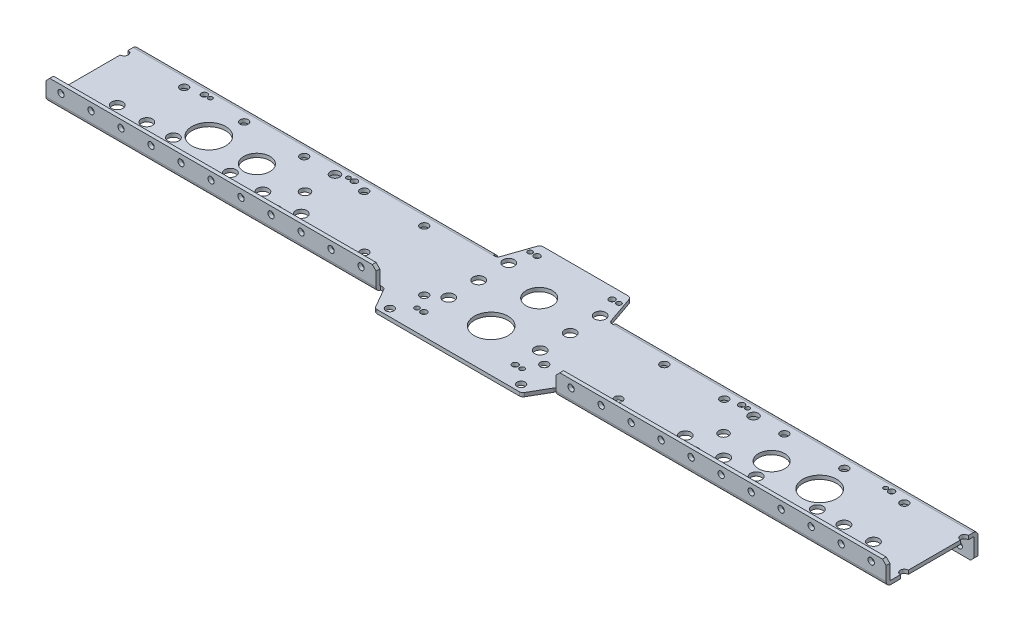
SolidWorks part; units mm, degrees
ref_plane "Front Plane" through (0, 0, 0) normal (0, 0, 1) x (1, 0, 0)
ref_plane "Top Plane" through (0, 0, 0) normal (0, 1, 0) x (1, 0, 0)
ref_plane "Right Plane" through (0, 0, 0) normal (1, 0, 0) x (0, 0, -1)
ref_plane "Plane1" through (0, 3.175, 0) normal (0, 1, 0) x (1, 0, 0)
sketch "Sketch1" plane through (0, 3.175, 0) normal (0, 1, 0) x (1, 0, 0)
  line L0 (50.8, -3.937) -> (355.6, -3.937)
  line L1 (355.6, -3.937) -> (355.6, 73.787)
  line L2 (355.6, 73.787) -> (50.8, 73.787)
  line L3 (50.8, 73.787) -> (50.8, -3.937)
extrude "Boss-Extrude1" add sketch "Sketch1" against normal blind 22.225
sketch "Sketch2" plane through (50.8, 0, 0) normal (-1, 0, 0) x (0, 0, 1)
  line L0 (3.937, -19.05) -> (3.937, 0)
  line L1 (3.937, 0) -> (-70.612, 0)
  line L2 (-70.612, 0) -> (-70.612, -19.05)
  line L3 (-70.612, -19.05) -> (3.937, -19.05)
extrude "Cut-Extrude1" cut sketch "Sketch2" against normal through all
sketch "Sketch3" plane through (355.6, 0, 0) normal (1, 0, 0) x (0, 0, -1)
  line L0 (69.85, 0) -> (-3.937, 0)
  line L1 (-3.937, 0) -> (-3.937, 3.175)
  line L2 (-3.937, 3.175) -> (69.85, 3.175)
  line L3 (69.85, 3.175) -> (69.85, 0)
extrude "Boss-Extrude2" add sketch "Sketch3" along normal blind 406.4
sketch "Sketch4" plane through (0, 0, -69.85) normal (0, 0, -1) x (-1, 0, 0)
  line L0 (-762, 0) -> (-762, 3.175)
  line L1 (-762, 3.175) -> (-457.2, 3.175)
  line L2 (-457.2, 3.175) -> (-457.2, 0)
  line L3 (-457.2, 0) -> (-762, 0)
extrude "Boss-Extrude3" add sketch "Sketch4" along normal blind 3.937
sketch "Sketch5" plane through (0, 0, 0) normal (0, -1, 0) x (1, 0, 0)
  line L0 (457.2, -70.612) -> (762, -70.612)
  line L1 (762, -70.612) -> (762, -73.787)
  line L2 (762, -73.787) -> (457.2, -73.787)
  line L3 (457.2, -73.787) -> (457.2, -70.612)
extrude "Boss-Extrude4" add sketch "Sketch5" along normal blind 19.05
sketch "Sketch6" plane through (0, 3.175, 0) normal (0, 1, 0) x (-1, 0, 0)
  line L0 (-482.6, 3.937) -> (-482.6, 0)
  line L1 (-482.6, 0) -> (-50.8, 0)
  line L2 (-50.8, 0) -> (-50.8, 3.937)
  line L3 (-50.8, 3.937) -> (-482.6, 3.937)
extrude "Cut-Extrude2" cut sketch "Sketch6" against normal through all
sketch "Sketch7" plane through (0, 3.175, 0) normal (0, 1, 0) x (-1, 0, 0)
  line L0 (-762, 3.937) -> (-482.6, 3.937)
  line L1 (-482.6, 3.937) -> (-482.6, 0.762)
  line L2 (-482.6, 0.762) -> (-762, 0.762)
  line L3 (-762, 0.762) -> (-762, 3.937)
extrude "Boss-Extrude5" add sketch "Sketch7" along normal blind 15.875
sketch "Sketch8" plane through (0, 0, 0) normal (0, 0, 1) x (1, 0, 0)
  line L0 (330.2, 3.175) -> (330.2, 0)
  line L1 (330.2, 0) -> (50.8, 0)
  line L2 (50.8, 0) -> (50.8, 3.175)
  line L3 (50.8, 3.175) -> (330.2, 3.175)
extrude "Boss-Extrude6" add sketch "Sketch8" along normal blind 3.937
sketch "Sketch9" plane through (0, 3.175, 0) normal (0, 1, 0) x (-1, 0, 0)
  line L0 (-50.8, 0.762) -> (-330.2, 0.762)
  line L1 (-330.2, 0.762) -> (-330.2, 3.937)
  line L2 (-330.2, 3.937) -> (-50.8, 3.937)
  line L3 (-50.8, 3.937) -> (-50.8, 0.762)
extrude "Boss-Extrude7" add sketch "Sketch9" along normal blind 15.875
sketch "Sketch10" plane through (0, 0, -69.85) normal (0, 0, -1) x (-1, 0, 0)
  line L0 (-368.2206, 0) -> (-444.5794, 0)
  line L1 (-444.5794, 0) -> (-444.5794, 3.175)
  line L2 (-444.5794, 3.175) -> (-368.2206, 3.175)
  line L3 (-368.2206, 3.175) -> (-368.2206, 0)
extrude "Boss-Extrude8" add sketch "Sketch10" along normal blind 27.432
sketch "Sketch11" plane through (0, 0, 0) normal (0, 0, 1) x (1, 0, 0)
  line L0 (468.4265, 0) -> (344.3735, 0)
  line L1 (344.3735, 0) -> (344.3735, 3.175)
  line L2 (344.3735, 3.175) -> (468.4265, 3.175)
  line L3 (468.4265, 3.175) -> (468.4265, 0)
extrude "Boss-Extrude9" add sketch "Sketch11" along normal blind 19.05
draft "Draft1" type of draft neutral plane draft angle 30 faces to draft 2 face at (344.3735, 1.5875, 9.525) face at (468.4265, 1.5875, 9.525) neutral plane through (0, 0, 19.05) neutral plane normal (0, 0, 1) parameters "D1"=30
draft "Draft2" type of draft neutral plane draft angle 19 faces to draft 2 face at (444.5794, 1.5875, -83.566) face at (368.2206, 1.5875, -83.566) neutral plane through (0, 0, -97.282) neutral plane normal (0, 0, -1) parameters "D1"=19
hole_wizard "M8 Clearance Hole1" positions "Sketch13" profile "Sketch12" hole size "M8" standard "ANSI Metric"
sketch "Sketch13" plane through (0, 0, 0) normal (0, -1, 0) x (-1, 0, 0)
  point P0 (-367.6757, 70.866)
  point P1 (-367.6757, 20.066)
  point P2 (-445.1243, 20.066)
  point P3 (-445.1243, 70.866)
  point P4 (-367.6757, 45.466)
  point P5 (-445.1243, 45.466)
  point P6 (-628.9477, 19.05)
  point P7 (-601.4385, 19.05)
  point P8 (-568.9249, 19.05)
  point P9 (-243.8751, 19.05)
  point P10 (-211.3615, 19.05)
  point P11 (-183.8523, 19.05)
  point P12 (-678.9442, 20.828)
  point P13 (-701.4504, 20.828)
  point P14 (-726.4609, 20.828)
  point P15 (-133.8558, 20.828)
  point P16 (-111.3496, 20.828)
  point P17 (-86.3391, 20.828)
sketch "Sketch12" plane through (367.6757, 0, -70.866) normal (1, 0, 0) x (0, 0, -1)
  line L0 (0, 0) -> (0, 19.05)
  line L1 (0, 19.05) -> (4.7625, 19.05)
  line L2 (4.7625, 19.05) -> (4.7625, 0)
  line L5 (4.7625, 0) -> (0, 0)
  line L11 (0, -6.35) -> (0, 107.95) construction
  dimension "Thru Hole Dia." = 9.525
  dimension "Thru Hole Depth" = 19.05
hole_wizard "M3.5 Clearance Hole1" positions "Sketch15" profile "Sketch14" hole size "M3.5" standard "ANSI Metric"
sketch "Sketch15" plane through (0, 0, 0) normal (0, -1, 0) x (-1, 0, 0)
  point P0 (-450.8881, -1.0389)
  point P1 (-361.9119, -1.0389)
  point P2 (-368.808, 87.8535)
  point P3 (-443.992, 87.8535)
sketch "Sketch14" plane through (450.8881, 0, 1.0389) normal (1, 0, 0) x (0, 0, -1)
  line L0 (0, 0) -> (0, 19.05)
  line L1 (0, 19.05) -> (2.032, 19.05)
  line L2 (2.032, 19.05) -> (2.032, 0)
  line L5 (2.032, 0) -> (0, 0)
  line L11 (0, -6.35) -> (0, 107.95) construction
  dimension "Thru Hole Dia." = 4.064
  dimension "Thru Hole Depth" = 19.05
hole_wizard "Hole1" positions "Sketch17" profile "Sketch16" legacy
sketch "Sketch17" plane through (0, 0, 0) normal (0, -1, 0) x (-1, 0, 0)
  point P0 (-583.5384, 62.23)
  point P1 (-229.2616, 11.43)
  point P2 (-229.2616, 62.23)
  point P3 (-229.2616, 36.83)
  point P4 (-583.5384, 36.83)
  point P5 (-583.5384, 11.43)
sketch "Sketch16" plane through (583.5384, 0, -62.23) normal (1, 0, 0) x (0, 0, -1)
  line L0 (0, 0) -> (0, 19.05)
  line L1 (0, 19.05) -> (4.064, 19.05)
  line L2 (4.064, 19.05) -> (4.064, 0)
  line L3 (4.064, 0) -> (0, 0)
  line L4 (0, 110) -> (0, -10) construction
  dimension "Diameter" = 8.128
  dimension "Depth" = 19.05
hole_wizard "M20 Clearance Hole1" positions "Sketch19" profile "Sketch18" hole size "M20" standard "ANSI Metric"
sketch "Sketch19" plane through (0, 0, 0) normal (0, -1, 0) x (-1, 0, 0)
  point P0 (-624.2546, 36.83)
  point P1 (-188.5454, 36.83)
  point P2 (-406.4, 57.9628)
sketch "Sketch18" plane through (624.2546, 0, -36.83) normal (1, 0, 0) x (0, 0, -1)
  line L0 (0, 0) -> (0, 19.05)
  line L1 (0, 19.05) -> (11.1125, 19.05)
  line L2 (11.1125, 19.05) -> (11.1125, 0)
  line L5 (11.1125, 0) -> (0, 0)
  line L11 (0, -6.35) -> (0, 107.95) construction
  dimension "Thru Hole Dia." = 22.225
  dimension "Thru Hole Depth" = 19.05
hole_wizard "M3 Clearance Hole1" positions "Sketch21" profile "Sketch20" hole size "M3" standard "ANSI Metric"
sketch "Sketch21" plane through (0, 0, 0) normal (0, -1, 0) x (-1, 0, 0)
  point P0 (-575.3596, 8.255)
  point P1 (-237.4404, 65.405)
  point P2 (-237.4404, 8.255)
  point P3 (-120.6004, 8.255)
  point P4 (-120.6004, 65.405)
  point P5 (-575.3596, 65.405)
  point P6 (-692.1996, 65.405)
  point P7 (-692.1996, 8.255)
sketch "Sketch20" plane through (575.3596, 0, -8.255) normal (1, 0, 0) x (0, 0, -1)
  line L0 (0, 0) -> (0, 19.05)
  line L1 (0, 19.05) -> (1.7859, 19.05)
  line L2 (1.7859, 19.05) -> (1.7859, 0)
  line L5 (1.7859, 0) -> (0, 0)
  line L11 (0, -6.35) -> (0, 107.95) construction
  dimension "Thru Hole Dia." = 3.5719
  dimension "Thru Hole Depth" = 19.05
hole_wizard "M25 Clearance Hole1" positions "Sketch23" profile "Sketch22" hole size "M25" standard "ANSI Metric"
sketch "Sketch23" plane through (0, 0, 0) normal (0, -1, 0) x (-1, 0, 0)
  point P0 (-664.9708, 36.83)
  point P1 (-147.8292, 36.83)
  point P2 (-406.4, 17.272)
sketch "Sketch22" plane through (664.9708, 0, -36.83) normal (1, 0, 0) x (0, 0, -1)
  line L0 (0, 0) -> (0, 19.05)
  line L1 (0, 19.05) -> (14.2875, 19.05)
  line L2 (14.2875, 19.05) -> (14.2875, 0)
  line L5 (14.2875, 0) -> (0, 0)
  line L11 (0, -6.35) -> (0, 107.95) construction
  dimension "Thru Hole Dia." = 28.575
  dimension "Thru Hole Depth" = 19.05
hole_wizard "Hole2" positions "Sketch25" profile "Sketch24" legacy
sketch "Sketch25" plane through (0, 0, 0) normal (0, -1, 0) x (-1, 0, 0)
  point P0 (-697.2796, 8.255)
  point P1 (-697.2796, 65.405)
  point P2 (-570.2796, 65.405)
  point P3 (-242.5204, 65.405)
  point P4 (-242.5204, 8.255)
  point P5 (-115.5204, 8.255)
  point P6 (-115.5204, 65.405)
  point P7 (-367.7539, -1.0389)
  point P8 (-445.0461, -1.0389)
  point P9 (-374.65, 87.8535)
  point P10 (-438.15, 87.8535)
  point P11 (-570.2796, 8.255)
sketch "Sketch24" plane through (697.2796, 0, -8.255) normal (1, 0, 0) x (0, 0, -1)
  line L0 (0, 0) -> (0, 19.05)
  line L1 (0, 19.05) -> (2.5527, 19.05)
  line L2 (2.5527, 19.05) -> (2.5527, 0)
  line L3 (2.5527, 0) -> (0, 0)
  line L4 (0, 110) -> (0, -10) construction
  dimension "Diameter" = 5.1054
  dimension "Depth" = 19.05
hole_wizard "M6 Clearance Hole1" positions "Sketch27" profile "Sketch26" hole size "M6" standard "ANSI Metric"
sketch "Sketch27" plane through (0, 0, 0) normal (0, -1, 0) x (-1, 0, 0)
  point P0 (-50.8, 62.23)
  point P1 (-762, 62.23)
  point P2 (-461.9625, -12.8905)
  point P3 (-350.8375, -12.8905)
  point P4 (-513.9255, 17.5473)
  point P5 (-298.8745, 17.5473)
  point P6 (-711.2, 11.43)
  point P7 (-660.4, 62.23)
  point P8 (-660.4, 11.43)
  point P9 (-609.6, 62.23)
  point P10 (-711.2, 62.23)
  point P11 (-152.4, 62.23)
  point P12 (-203.2, 11.43)
  point P13 (-203.2, 62.23)
  point P14 (-254, 11.43)
  point P15 (-101.6, 11.43)
  point P16 (-101.6, 62.23)
  point P17 (-152.4, 11.43)
  point P18 (-254, 62.23)
  point P19 (-304.8, 62.23)
  point P20 (-355.6, 11.43)
  point P21 (-457.2, 11.43)
  point P22 (-609.6, 11.43)
  point P23 (-558.8, 62.23)
  point P24 (-558.8, 11.43)
  point P25 (-508, 62.23)
sketch "Sketch26" plane through (50.8, 0, -62.23) normal (1, 0, 0) x (0, 0, -1)
  line L0 (0, 0) -> (0, 19.05)
  line L1 (0, 19.05) -> (3.3782, 19.05)
  line L2 (3.3782, 19.05) -> (3.3782, 0)
  line L5 (3.3782, 0) -> (0, 0)
  line L11 (0, -6.35) -> (0, 107.95) construction
  dimension "Thru Hole Dia." = 6.7564
  dimension "Thru Hole Depth" = 19.05
hole_wizard "M6 Clearance Hole2" positions "Sketch29" profile "Sketch28" hole size "M6" standard "ANSI Metric"
sketch "Sketch29" plane through (0, 3.175, 0) normal (0, 1, 0) x (1, 0, 0)
  point P0 (50.8, 11.43)
  point P1 (762, 11.43)
sketch "Sketch28" plane through (50.8, 3.175, -11.43) normal (1, 0, 0) x (0, 0, 1)
  line L0 (0, 0) -> (0, 22.225)
  line L1 (0, 22.225) -> (3.3782, 22.225)
  line L2 (3.3782, 22.225) -> (3.3782, 0)
  line L5 (3.3782, 0) -> (0, 0)
  line L11 (0, -6.35) -> (0, 107.95) construction
  dimension "Thru Hole Dia." = 6.7564
  dimension "Thru Hole Depth" = 22.225
hole_wizard "M5 Clearance Hole1" positions "Sketch31" profile "Sketch30" hole size "M5" standard "ANSI Metric"
sketch "Sketch31" plane through (0, 0, 3.937) normal (0, 0, 1) x (1, 0, 0)
  point P0 (495.3, 12.7)
  point P1 (520.7, 12.7)
  point P2 (546.1, 12.7)
  point P3 (571.5, 12.7)
  point P4 (596.9, 12.7)
  point P5 (622.3, 12.7)
  point P6 (647.7, 12.7)
  point P7 (673.1, 12.7)
  point P8 (698.5, 12.7)
  point P9 (723.9, 12.7)
  point P10 (749.3, 12.7)
  point P11 (317.5, 12.7)
  point P12 (292.1, 12.7)
  point P13 (266.7, 12.7)
  point P14 (241.3, 12.7)
  point P15 (215.9, 12.7)
  point P16 (190.5, 12.7)
  point P17 (165.1, 12.7)
  point P18 (139.7, 12.7)
  point P19 (114.3, 12.7)
  point P20 (88.9, 12.7)
  point P21 (63.5, 12.7)
sketch "Sketch30" plane through (495.3, 12.7, 3.937) normal (1, 0, 0) x (0, -1, 0)
  line L0 (0, 0) -> (0, 101.219)
  line L1 (0, 101.219) -> (2.667, 101.219)
  line L2 (2.667, 101.219) -> (2.667, 0)
  line L5 (2.667, 0) -> (0, 0)
  line L11 (0, -6.35) -> (0, 107.95) construction
  dimension "Thru Hole Dia." = 5.334
  dimension "Thru Hole Depth" = 101.219
hole_wizard "M5 Clearance Hole2" positions "Sketch33" profile "Sketch32" hole size "M5" standard "ANSI Metric"
sketch "Sketch33" plane through (0, 0, -70.612) normal (0, 0, 1) x (1, 0, 0)
  point P0 (342.9, -12.7)
  point P1 (317.5, -12.7)
  point P2 (292.1, -12.7)
  point P3 (266.7, -12.7)
  point P4 (241.3, -12.7)
  point P5 (215.9, -12.7)
  point P6 (190.5, -12.7)
  point P7 (165.1, -12.7)
  point P8 (139.7, -12.7)
  point P9 (114.3, -12.7)
  point P10 (88.9, -12.7)
  point P11 (63.5, -12.7)
  point P12 (469.9, -12.7)
  point P13 (495.3, -12.7)
  point P14 (520.7, -12.7)
  point P15 (546.1, -12.7)
  point P16 (571.5, -12.7)
  point P17 (596.9, -12.7)
  point P18 (622.3, -12.7)
  point P19 (647.7, -12.7)
  point P20 (673.1, -12.7)
  point P21 (698.5, -12.7)
  point P22 (723.9, -12.7)
  point P23 (749.3, -12.7)
sketch "Sketch32" plane through (342.9, -12.7, -70.612) normal (1, 0, 0) x (0, -1, 0)
  line L0 (0, 0) -> (0, 26.67)
  line L1 (0, 26.67) -> (2.667, 26.67)
  line L2 (2.667, 26.67) -> (2.667, 0)
  line L5 (2.667, 0) -> (0, 0)
  line L11 (0, -6.35) -> (0, 107.95) construction
  dimension "Thru Hole Dia." = 5.334
  dimension "Thru Hole Depth" = 26.67
chamfer "Chamfer1" distance 3.175 angle 45 8 edges at (330.2, 19.05, 2.3495) (457.2, -19.05, -72.1995) (762, 19.05, 2.3495) (50.8, -19.05, -72.1995) (355.6, -19.05, -72.1995) (482.6, 19.05, 2.3495) (50.8, 19.05, 2.3495) (762, -19.05, -72.1995)
fillet "Fillet1" radius 0.762 4 edges at (190.5, 3.175, 0.762) (622.3, 3.175, 0.762) (203.2, 0, -70.612) (609.6, 0, -70.612)
fillet "Fillet2" radius 3.175 8 edges at (333.375, 1.5875, 0) (468.4265, 1.5875, 19.05) (479.425, 1.5875, 0) (368.2206, 1.5875, -97.282) (344.3735, 1.5875, 19.05) (444.5794, 1.5875, -97.282) (454.025, 1.5875, -69.85) (358.775, 1.5875, -69.85)
fillet "Fillet3" radius 3.937 4 edges at (190.5, 0, 3.937) (622.3, 0, 3.937) (203.2, 3.175, -73.787) (609.6, 3.175, -73.787)
